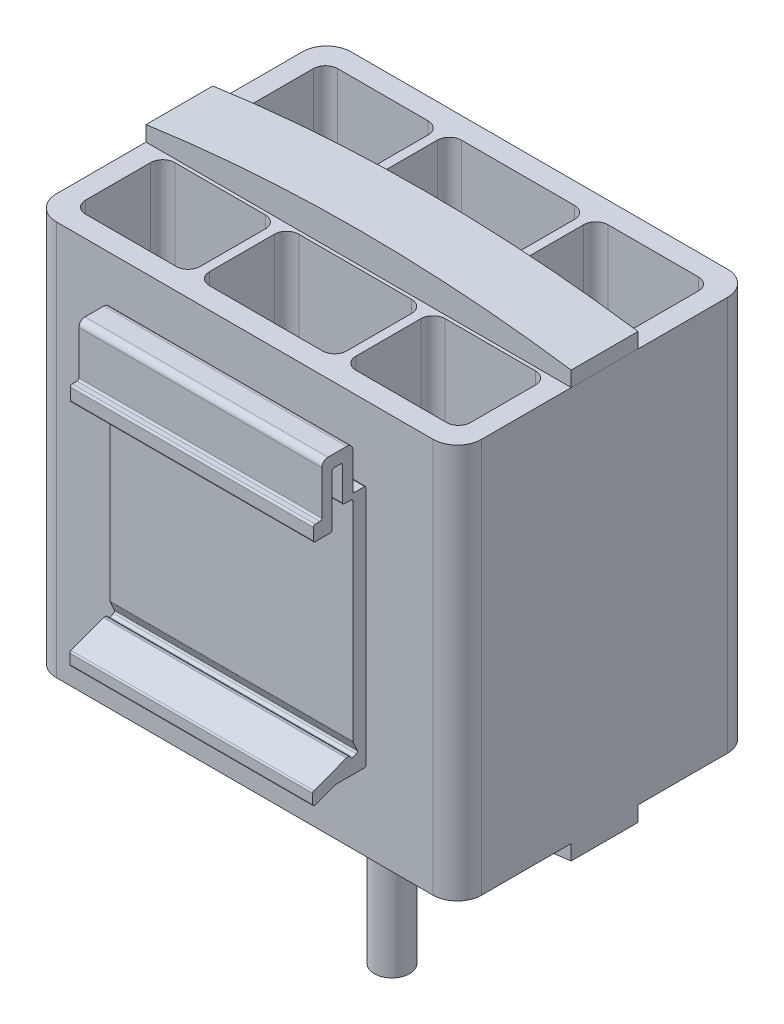
SolidWorks part; units mm, degrees
ref_plane "Спереди" through (0, 0, 0) normal (0, 0, 1) x (1, 0, 0)
ref_plane "Сверху" through (0, 0, 0) normal (0, 1, 0) x (1, 0, 0)
ref_plane "Справа" through (0, 0, 0) normal (1, 0, 0) x (0, 0, -1)
sketch "Эскиз1" plane through (0, 0, 0) normal (0, 0, 1) x (1, 0, 0)
  line L1 (-35, -32.5) -> (35, -32.5)
  line L2 (-35, -32.5) -> (-35, 32.5)
  line L3 (-35, 32.5) -> (35, 32.5)
  line L4 (35, -32.5) -> (35, 32.5)
  line L5 (-35, -32.5) -> (35, 32.5) construction
  line L6 (-35, 32.5) -> (35, -32.5) construction
  point P0 (0, 0)
  dimension "D1" = 70
  dimension "D2" = 65
extrude "Бобышка-Вытянуть1" add sketch "Эскиз1" along normal blind 48.5
sketch "Эскиз2" plane through (0, 32.5, 0) normal (0, 1, 0) x (1, 0, 0)
  line L0 (0, 0) -> (0, -10.85) construction
  line L1 (-11.3, -3.5) -> (11.3, -3.5)
  line L2 (-11.3, -3.5) -> (-11.3, -18.2)
  line L3 (-11.3, -18.2) -> (11.3, -18.2)
  line L4 (11.3, -3.5) -> (11.3, -18.2)
  line L5 (-11.3, -3.5) -> (11.3, -18.2) construction
  line L6 (-11.3, -18.2) -> (11.3, -3.5) construction
  line L7 (12.8, -3.5) -> (31.7, -3.5)
  line L8 (12.8, -3.5) -> (12.8, -18.2)
  line L9 (12.8, -18.2) -> (31.7, -18.2)
  line L10 (31.7, -3.5) -> (31.7, -18.2)
  line L11 (12.8, -3.5) -> (31.7, -18.2) construction
  line L12 (12.8, -18.2) -> (31.7, -3.5) construction
  line L13 (-31.7, -3.5) -> (-12.8, -3.5)
  line L14 (-31.7, -3.5) -> (-31.7, -18.2)
  line L15 (-31.7, -18.2) -> (-12.8, -18.2)
  line L16 (-12.8, -3.5) -> (-12.8, -18.2)
  line L17 (-31.7, -3.5) -> (-12.8, -18.2) construction
  line L18 (-31.7, -18.2) -> (-12.8, -3.5) construction
  line L19 (35, 0) -> (-35, 0) construction
  line L20 (-35, -24.25) -> (35, -24.25) construction
  line L21 (-35, -48.5) -> (-35, 0) construction
  line L22 (35, -48.5) -> (35, 0) construction
  line L23 (12.8, -30.3) -> (31.7, -30.3)
  line L24 (31.7, -45) -> (31.7, -30.3)
  line L25 (12.8, -45) -> (31.7, -45)
  line L26 (12.8, -45) -> (12.8, -30.3)
  line L27 (-11.3, -30.3) -> (11.3, -30.3)
  line L28 (11.3, -45) -> (11.3, -30.3)
  line L29 (-11.3, -45) -> (11.3, -45)
  line L30 (-11.3, -45) -> (-11.3, -30.3)
  line L31 (-31.7, -30.3) -> (-12.8, -30.3)
  line L32 (-12.8, -45) -> (-12.8, -30.3)
  line L33 (-31.7, -45) -> (-12.8, -45)
  line L34 (-31.7, -45) -> (-31.7, -30.3)
  point P0 (0, -10.85)
  point P5 (22.25, -10.85)
  point P10 (-22.25, -10.85)
  dimension "D1" = 22.6
  dimension "D2" = 18.9
  dimension "D3" = 1.5
  dimension "D4" = 1.5
  dimension "D5" = 3.5
  dimension "D6" = 14.7
extrude "Вырез-Вытянуть1" cut sketch "Эскиз2" against normal up to next
sketch "Эскиз3" plane through (0, 32.5, 0) normal (0, 1, 0) x (1, 0, 0)
  line L0 (35, -48.5) -> (35, 0) construction
  line L1 (-35, -29.75) -> (35, -29.75)
  line L2 (-35, -29.75) -> (-35, -18.75)
  line L3 (-35, -18.75) -> (35, -18.75)
  line L4 (35, -29.75) -> (35, -18.75)
  line L5 (-35, -29.75) -> (35, -18.75) construction
  line L6 (-35, -18.75) -> (35, -29.75) construction
  line L7 (0, 0) -> (0, -24.25) construction
  line L8 (35, 0) -> (-35, 0) construction
  line L9 (0, -24.25) -> (35, -24.25) construction
  point P0 (0, -24.25)
  point P11 (0, -24.4908)
  point P13 (35, -26.6567)
  point P14 (35, -27.6078)
  point P15 (35, -24.25)
  dimension "D1" = 11
extrude "Бобышка-Вытянуть2" add sketch "Эскиз3" along normal blind 5 separate body
sketch "Эскиз4" plane through (0, 0, 29.75) normal (0, 0, 1) x (1, 0, 0)
  line L0 (-35, 37.5) -> (-35, 32.5) construction
  line L1 (35, 37.5) -> (35, 32.5) construction
  line L2 (-35, 37.5) -> (35, 37.5) construction
  line L3 (-35, 32.5) -> (35, 32.5) construction
  line L4 (-35, 35) -> (-35, 41)
  line L5 (-35, 41) -> (35, 41)
  line L6 (35, 41) -> (35, 35)
  arc A0 (-35, 35) -> (35, 35) centre (0, -208.75) cw
  point P3 (0, 37.5)
  dimension "D1" = 2.5
  dimension "D2" = 6
extrude "Вырез-Вытянуть4" cut sketch "Эскиз4" against normal up to surface (11 mm away) up to face at (0, 35, 18.75)
ref_plane "Плоскость1" through (0, 0, 0) normal (0, 1, 0) x (1, 0, 0)
mirror "Зеркальное отражение2" about plane through (0, 0, 0) normal (0, 1, 0) of "Вырез-Вытянуть4", "Бобышка-Вытянуть2"
ref_plane "Плоскость2" through (0, 0, 24.25) normal (0, 0, -1) x (-1, 0, 0)
sketch "Эскиз5" plane through (0, 0, 24.25) normal (0, 0, -1) x (-1, 0, 0)
  line L7 (-11.5, -46.8774) -> (-17.5, -36.8774)
  line L9 (-11.5, -46.8774) -> (-6.15, -46.8774)
  line L10 (-6.15, -46.8774) -> (-6.15, -49.8774)
  line L11 (-6.15, -49.8774) -> (6.15, -49.8774)
  line L12 (6.15, -46.8774) -> (6.15, -49.8774)
  line L13 (0, 0) -> (0, -49.8774) construction
  line L14 (11.5, -46.8774) -> (6.15, -46.8774)
  line L15 (11.5, -46.8774) -> (17.5, -36.8774)
  arc A0 (-35, -35) -> (35, -35) centre (0, 208.75) ccw construction
  arc A1 (-17.5, -36.8774) -> (17.5, -36.8774) centre (0, 208.75) ccw
  dimension "D1" = 6.15
  dimension "D2" = 11.5
  dimension "D3" = 17.5
  dimension "D4" = 10
  dimension "D5" = 3
extrude "Бобышка-Вытянуть3" add sketch "Эскиз5" along normal up to surface and the other way up to surface up to face at (0, -34.375, 18.75) other way up to face at (0, -34.375, 29.75)
ref_plane "Плоскость3" through (0, 0, 0) normal (-1, 0, 0) x (0, 0, 1)
sketch "Эскиз11" plane through (0, 0, 0) normal (-1, 0, 0) x (0, 0, 1)
  line L0 (48.8, -19.7) -> (53.4465, -19.7)
  line L1 (53.5502, -19.7185) -> (56.8963, -20.9513)
  line L2 (57.3, -20.6698) -> (57.3, -19.0712)
  line L3 (57.1037, -18.7897) -> (51.7533, -16.8185)
  line L4 (51.6496, -16.8) -> (51.3956, -16.8)
  line L5 (51.1229, -16.975) -> (51.0531, -17.1273)
  line L6 (50.6554, -17.275) -> (50.1099, -17.025)
  line L7 (49.9622, -16.6273) -> (50.6727, -15.0772)
  line L8 (50.7, -14.9522) -> (50.7, 19.3)
  line L9 (51, 19.6) -> (52.1, 19.6)
  line L10 (52.4, 19.9) -> (52.4, 25.3)
  line L11 (52.7, 25.6) -> (53.8, 25.6)
  line L12 (54.1, 25.3) -> (54.1, 16.9)
  line L13 (54.4, 16.6) -> (56.9, 16.6)
  line L14 (57.2, 16.9) -> (57.2, 18.8)
  line L15 (56.9, 19.1) -> (56.1, 19.1)
  line L16 (55.8, 19.4) -> (55.8, 26.6)
  line L17 (54.8, 27.6) -> (51.7, 27.6)
  line L18 (50.7, 26.6) -> (50.7, 20.7)
  line L19 (50.4, 20.4) -> (48.8, 20.4)
  line L20 (48.5, 20.1) -> (48.5, -19.4)
  line L21 (48.5, 32.5) -> (48.5, -32.5) construction
  line L22 (48.5, 32.5) -> (0, 32.5) construction
  arc A0 (48.8, -19.7) -> (48.5, -19.4) centre (48.8, -19.4) cw
  arc A1 (53.4465, -19.7) -> (53.5502, -19.7185) centre (53.4465, -20) cw
  arc A2 (57.3, -19.0712) -> (57.1037, -18.7897) centre (57, -19.0712) ccw
  arc A3 (56.8963, -20.9513) -> (57.3, -20.6698) centre (57, -20.6698) ccw
  arc A4 (51.7533, -16.8185) -> (51.6496, -16.8) centre (51.6496, -17.1) ccw
  arc A5 (51.3956, -16.8) -> (51.1229, -16.975) centre (51.3956, -17.1) ccw
  arc A6 (50.6727, -15.0772) -> (50.7, -14.9522) centre (50.4, -14.9522) ccw
  arc A7 (50.1099, -17.025) -> (49.9622, -16.6273) centre (50.2349, -16.7523) cw
  arc A8 (51.0531, -17.1273) -> (50.6554, -17.275) centre (50.7804, -17.0023) cw
  arc A9 (54.1, 16.9) -> (54.4, 16.6) centre (54.4, 16.9) ccw
  arc A10 (56.9, 16.6) -> (57.2, 16.9) centre (56.9, 16.9) ccw
  arc A11 (57.2, 18.8) -> (56.9, 19.1) centre (56.9, 18.8) ccw
  arc A12 (56.1, 19.1) -> (55.8, 19.4) centre (56.1, 19.4) cw
  arc A13 (48.8, 20.4) -> (48.5, 20.1) centre (48.8, 20.1) ccw
  arc A14 (50.7, 20.7) -> (50.4, 20.4) centre (50.4, 20.7) cw
  arc A15 (50.7, 19.3) -> (51, 19.6) centre (51, 19.3) cw
  arc A16 (52.1, 19.6) -> (52.4, 19.9) centre (52.1, 19.9) ccw
  arc A17 (52.4, 25.3) -> (52.7, 25.6) centre (52.7, 25.3) cw
  arc A18 (53.8, 25.6) -> (54.1, 25.3) centre (53.8, 25.3) cw
  arc A19 (51.7, 27.6) -> (50.7, 26.6) centre (51.7, 26.6) ccw
  arc A20 (55.8, 26.6) -> (54.8, 27.6) centre (54.8, 26.6) ccw
  point P21 (53.25, 25.6)
  point P22 (53.25, 27.6)
  point P65 (48.5, 20.1)
  dimension "D7" = 0.3
  dimension "D8" = 1
  dimension "D1" = 2.1
  dimension "D2" = 2.2
  dimension "D3" = 47.3
  dimension "D4" = 6.5
  dimension "D5" = 2
  dimension "D6" = 11
  dimension "D9" = 7.2
  dimension "D10" = 12.4
extrude "Бобышка-Вытянуть6" add sketch "Эскиз11" along normal mid plane 40
fillet "Скругление1" radius 4 4 edges at (35, 0, 0) (35, 0, 48.5) (-35, 0, 0) (-35, 0, 48.5)
fillet "Скругление2" radius 2 24 edges at (-12.8, 0, 3.5) (-12.8, 0, 18.2) (-31.7, 0, 18.2) (-31.7, 0, 3.5) (-11.3, 0, 3.5) (-11.3, 0, 18.2) (11.3, 0, 18.2) (11.3, 0, 3.5) (31.7, 0, 18.2) (12.8, 0, 18.2) (12.8, 0, 3.5) (31.7, 0, 3.5) (31.7, 0, 30.3) (12.8, 0, 30.3) (12.8, 0, 45) (31.7, 0, 45) (11.3, 0, 45) (11.3, 0, 30.3) (-11.3, 0, 30.3) (-11.3, 0, 45) (-12.8, 0, 45) (-12.8, 0, 30.3) (-31.7, 0, 30.3) (-31.7, 0, 45)
sketch "Эскиз13" plane through (0, -49.8774, 0) normal (0, -1, 0) x (1, 0, 0)
  line L0 (-35, 29.75) -> (35, 29.75) construction
  line L1 (0, 30.3) -> (0, 24.25) construction
  line L2 (-9.3, 30.3) -> (9.3, 30.3) construction
  line L3 (0, 24.25) -> (6.15, 24.25) construction
  line L4 (6.15, 18.75) -> (6.15, 29.75) construction
  circle A0 centre (0, 24.25) radius 5.5
extrude "Вырез-Вытянуть8" cut sketch "Эскиз13" against normal up to surface (3 mm away) flip side to cut up to face at (-8.825, -46.8774, 24.25)
sketch "Эскиз14" plane through (0, -49.8774, 0) normal (0, -1, 0) x (1, 0, 0)
  circle A0 centre (0, 24.25) radius 2.9
  dimension "D1" = 5.8
extrude "Бобышка-Вытянуть7" add sketch "Эскиз14" along normal blind 20
